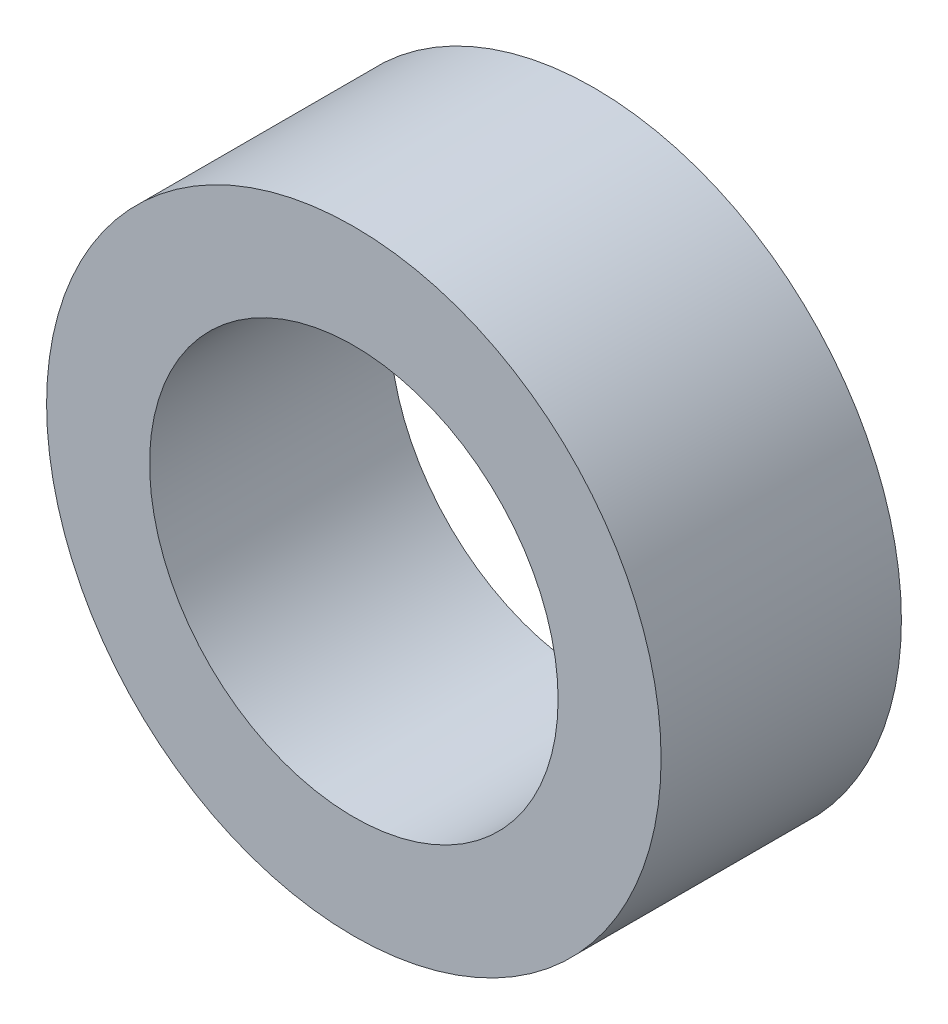
SolidWorks part; units mm, degrees
ref_plane "前视基准面" through (0, 0, 0) normal (0, 0, 1) x (1, 0, 0)
ref_plane "上视基准面" through (0, 0, 0) normal (0, 1, 0) x (1, 0, 0)
ref_plane "右视基准面" through (0, 0, 0) normal (1, 0, 0) x (0, 0, -1)
sketch "草图1" plane through (0, 0, 0) normal (0, 0, 1) x (1, 0, 0)
  circle A0 centre (0, 0) radius 8.95
  dimension "D1" = 17.9
extrude "拉伸-薄壁1" add sketch "草图1" along normal blind 7 thin thin type one direction reverse wall 3
